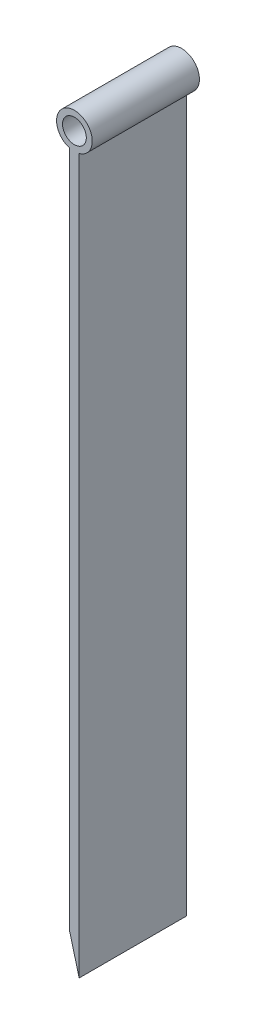
SolidWorks part; units mm, degrees
ref_plane "Alzado" through (0, 0, 0) normal (0, 0, 1) x (1, 0, 0)
ref_plane "Planta" through (0, 0, 0) normal (0, 1, 0) x (1, 0, 0)
ref_plane "Vista lateral" through (0, 0, 0) normal (1, 0, 0) x (0, 0, -1)
sketch "Croquis3" plane through (0, 0, 0) normal (0, 0, 1) x (1, 0, 0)
  line L0 (0, 149.8858) -> (0, 0)
  line L1 (0, 0) -> (-2, 7.5)
  line L2 (-2, 7.5) -> (-2, 149.8858)
  circle A0 centre (-1, 153.5) radius 3.75
  circle A1 centre (-1, 153.5) radius 2.5
  dimension "D4" = 5
  dimension "D5" = 7.5
  dimension "D3" = 2
extrude "Saliente-Extruir1" add sketch "Croquis3" along normal blind 22.5 contours A0 A1 | A0 L2 L1 L0
